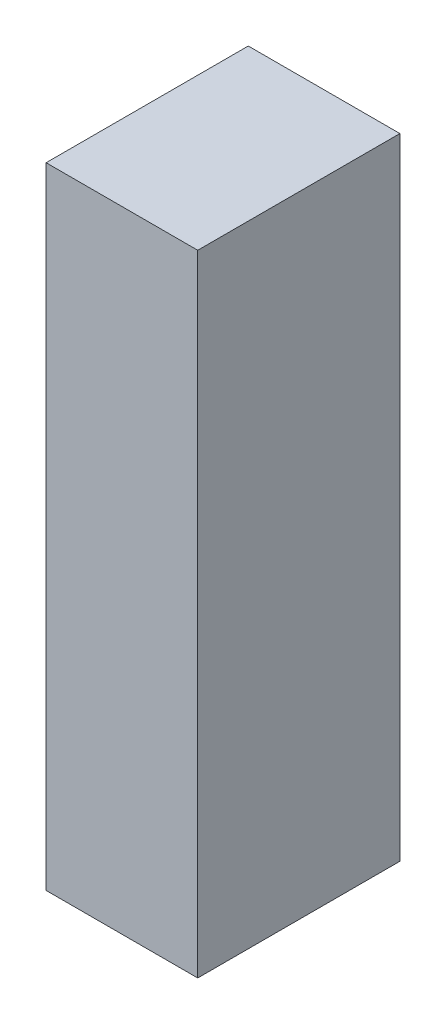
SolidWorks part; units mm, degrees
ref_plane "Front Plane" through (0, 0, 0) normal (0, 0, 1) x (1, 0, 0)
ref_plane "Top Plane" through (0, 0, 0) normal (0, 1, 0) x (1, 0, 0)
ref_plane "Right Plane" through (0, 0, 0) normal (1, 0, 0) x (0, 0, -1)
sketch "Sketch1" plane through (0, 0, 0) normal (0, 0, 1) x (1, 0, 0)
  line L1 (0, 0) -> (25.5, 0)
  line L2 (0, 0) -> (0, 106)
  line L3 (0, 106) -> (25.5, 106)
  line L4 (25.5, 0) -> (25.5, 106)
  dimension "D1" = 106
  dimension "D2" = 25.5
extrude "Boss-Extrude1" add sketch "Sketch1" along normal blind 34
